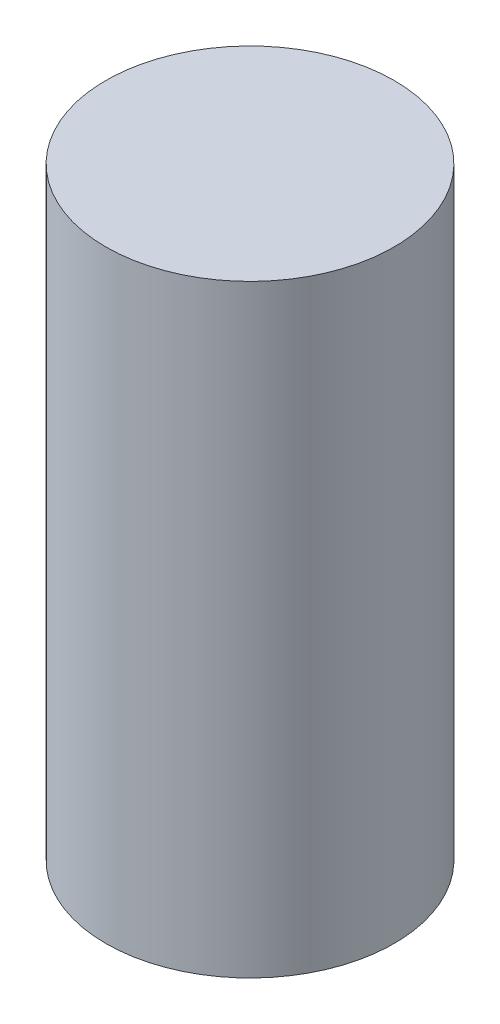
SolidWorks part; units mm, degrees
material "Reg 1 mat'l"
ref_plane "Front Plane" through (0, 0, 0) normal (0, 0, 1) x (1, 0, 0)
ref_plane "Top Plane" through (0, 0, 0) normal (0, 1, 0) x (1, 0, 0)
ref_plane "Right Plane" through (0, 0, 0) normal (1, 0, 0) x (0, 0, -1)
sketch "Sketch1" plane through (0, 0, 0) normal (0, 1, 0) x (1, 0, 0)
  circle A0 centre (0, 0) radius 14.2875
  dimension "D1" = 28.575
extrude "Boss-Extrude1" add sketch "Sketch1" along normal blind 59.7804
